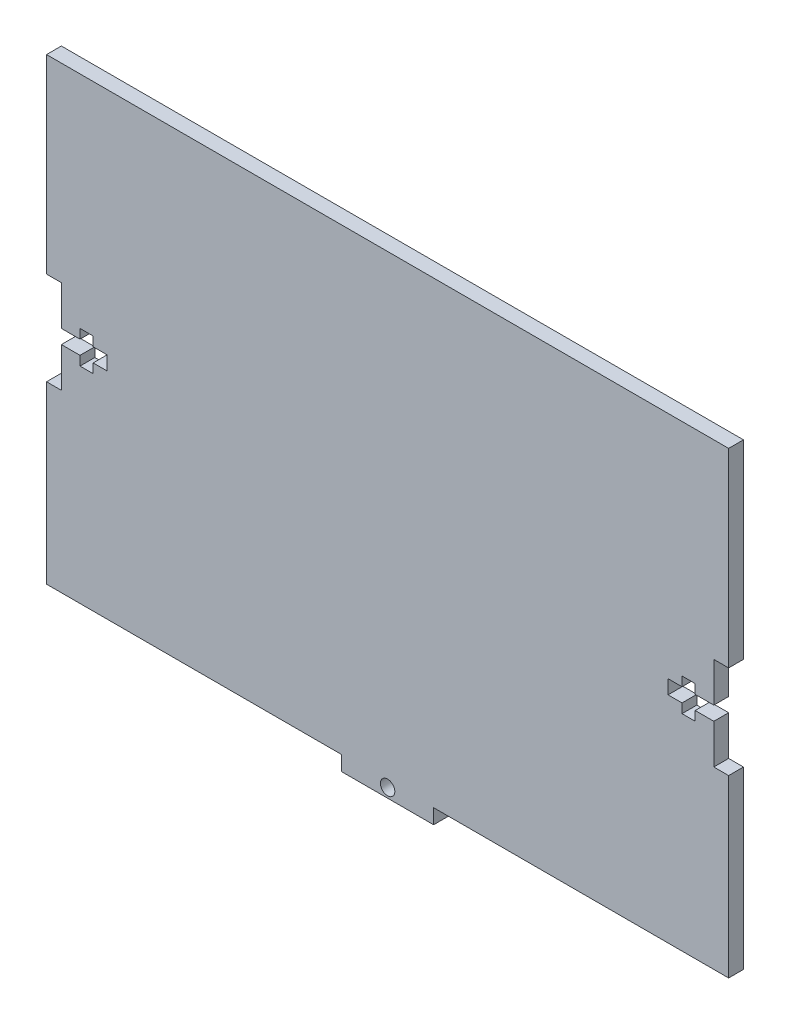
SolidWorks part; units mm, degrees
ref_plane "Front Plane" through (0, 0, 0) normal (0, 0, 1) x (1, 0, 0)
ref_plane "Top Plane" through (0, 0, 0) normal (0, 1, 0) x (1, 0, 0)
ref_plane "Right Plane" through (0, 0, 0) normal (1, 0, 0) x (0, 0, -1)
sketch "Sketch1" plane through (0, 0, 0) normal (0, 0, 1) x (1, 0, 0)
  line L1 (-73.18, 50.8) -> (73.18, 50.8)
  line L2 (-73.18, 50.8) -> (-73.18, -50.8)
  line L3 (-73.18, -50.8) -> (73.18, -50.8)
  line L4 (73.18, 50.8) -> (73.18, -50.8)
  point P0 (0, 0)
  dimension "D1" = 146.36
  dimension "D2" = 101.6
  dimension "D3" = 73.18
  dimension "D4" = 50.8
extrude "Boss-Extrude1" add sketch "Sketch1" along normal blind 3.18
sketch "Sketch2" plane through (0, 0, 3.18) normal (0, 0, 1) x (1, 0, 0)
  line L0 (0, 0) -> (50000, 0) construction
  line L1 (73.18, -50.8) -> (73.18, 50.8) construction
  line L2 (-73.18, 50.8) -> (-73.18, -50.8) construction
  line L3 (-73.18, 10) -> (-70, 10)
  line L4 (-73.18, 10) -> (-73.18, -10)
  line L5 (-73.18, -10) -> (-70, -10)
  line L6 (-70, 10) -> (-70, -10)
  line L8 (-73.18, 1.5) -> (-60.18, 1.5)
  line L9 (-73.18, 1.5) -> (-73.18, -1.5)
  line L10 (-73.18, -1.5) -> (-60.18, -1.5)
  line L11 (-60.18, 1.5) -> (-60.18, -1.5)
  line L12 (-66, 3.5) -> (-63.18, 3.5)
  line L13 (-66, 3.5) -> (-66, -3.5)
  line L14 (-66, -3.5) -> (-63.18, -3.5)
  line L15 (-63.18, 3.5) -> (-63.18, -3.5)
  point P5 (73.18, 0)
  point P20 (-70, 0)
  line M16 (-73.18, 50.8) -> (-73.18, -50.8)
  dimension "D1" = 20
  dimension "D2" = 3.18
  dimension "D3" = 10
  dimension "D4" = 1.5
  dimension "D5" = 3
  dimension "D6" = 13
  dimension "D7" = 2.82
  dimension "D8" = 7
  dimension "D9" = 3.5
  dimension "D10" = 4
extrude "Cut-Extrude1" cut sketch "Sketch2" against normal through all both and the other way through all contours L8 L6 L3 M16 | L4 L0 L6 L8 | L0 L9 L10 L6 | L10 L5 L6 M16 | L6 L0 L13 L8 | L0 L6 L10 L13 | L15 L12 L13 L8 | L13 L0 L15 L8 | L0 L13 L10 L15 | L15 L10 L13 L14 | L15 L0 L11 L8 | L0 L15 L10 L11
mirror "Mirror1" about plane through (0, 0, 0) normal (1, 0, 0) of "Cut-Extrude1"
sketch "Sketch3" plane through (0, 0, 3.18) normal (0, 0, 1) x (1, 0, 0)
  line L0 (0, 0) -> (0, -50000) construction
  line L7 (-73.18, -50.8) -> (-9.875, -50.8)
  line L8 (-73.18, -50.8) -> (-73.18, -47.62)
  line L9 (-73.18, -47.62) -> (-9.875, -47.62)
  line L10 (-9.875, -50.8) -> (-9.875, -47.62)
  dimension "D1" = 63.305
  dimension "D2" = 3.18
extrude "Cut-Extrude2" cut sketch "Sketch3" against normal through all both and the other way through all
mirror "Mirror2" about plane through (0, 0, 0) normal (1, 0, 0) of "Cut-Extrude2"
sketch "Sketch4" plane through (0, 0, 3.18) normal (0, 0, 1) x (1, 0, 0)
  line L0 (-9.875, -50.8) -> (9.875, -50.8) construction
  circle A0 centre (0, -48.8) radius 1.55
  dimension "D1" = 3.1
  dimension "D2" = 2
  dimension "D3" = 9.875
extrude "Cut-Extrude3" cut sketch "Sketch4" against normal through all both and the other way through all contours A0
sketch "Sketch6" plane through (0, 0, 0) normal (0, 0, -1) x (-1, 0, 0)
  circle A0 centre (46.3033, -15.3173) radius 1.4
  circle A1 centre (24.8033, -29.0673) radius 1.4
  circle A2 centre (24.8033, -1.5673) radius 1.4
  dimension "D1" = 2.8
  dimension "D2" = 2.8
  dimension "D3" = 2.8
